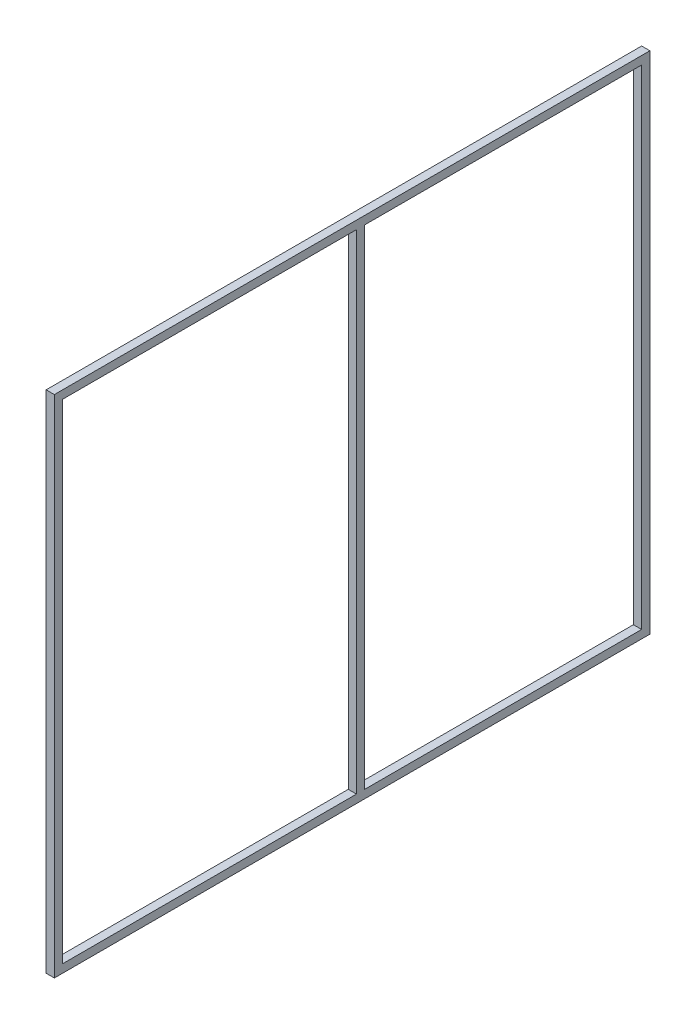
SolidWorks part; units mm, degrees
ref_plane "Front Plane" through (0, 0, 0) normal (0, 0, 1) x (1, 0, 0)
ref_plane "Top Plane" through (0, 0, 0) normal (0, 1, 0) x (1, 0, 0)
ref_plane "Right Plane" through (0, 0, 0) normal (1, 0, 0) x (0, 0, -1)
sketch "Sketch1" plane through (0, 0, 0) normal (1, 0, 0) x (0, 0, -1)
  line L0 (-559.125, -472.0175) -> (-559.125, 472.0175)
  line L2 (-575, -487.8925) -> (-575, 487.8925)
  line L3 (-575, 487.8925) -> (575, 487.8925)
  line L4 (575, -487.8925) -> (575, 487.8925)
  line L5 (-575, -487.8925) -> (575, 487.8925) construction
  line L6 (-575, 487.8925) -> (575, -487.8925) construction
  line L7 (-559.125, 472.0175) -> (559.125, 472.0175)
  line L8 (559.125, -472.0175) -> (559.125, 472.0175)
  line L9 (-575, -487.8925) -> (-559.125, -487.8925)
  line L10 (559.125, -487.8925) -> (575, -487.8925)
  line L11 (-559.125, -487.8925) -> (559.125, -487.8925)
  line L12 (-559.125, -472.0175) -> (559.125, -472.0175)
  line L14 (559.125, -487.8925) -> (559.125, 472.0175) construction
  line L15 (-559.125, -487.8925) -> (-559.125, 472.0175) construction
  point P0 (0, 0)
  point P7 (0, 0)
  dimension "D1" = 1150
  dimension "D2" = 975.785
  dimension "D4" = 15.875
  dimension "D3" = 15.875
extrude "Boss-Extrude1" add sketch "Sketch1" along normal blind 15.875
sketch "Sketch2" [suppressed] plane through (0, -487.8925, 0) normal (0, -1, 0) x (1, 0, 0)
  line L0 (66.5, 469.5) -> (66.5, 555.5) construction
  line L1 (0, 562.5) -> (66.5, 562.5)
  line L2 (0, 562.5) -> (0, 462.5)
  line L3 (0, 462.5) -> (66.5, 462.5)
  line L4 (66.5, 562.5) -> (66.5, 462.5)
  line L5 (89, 512.5) -> (63.5, 512.5) construction
  line L6 (15.875, 546.625) -> (50.625, 546.625)
  line L7 (50.625, 546.625) -> (50.625, 478.375)
  line L8 (15.875, 478.375) -> (50.625, 478.375)
  line L9 (15.875, 546.625) -> (15.875, 478.375)
  line L10 (0, 575) -> (0, -575) construction
  point P7 (66.5, 512.5)
  point P17 (33.25, 462.5)
  dimension "D2" = 100
  dimension "D1" = 15.875
sketch "Sketch3" plane through (0, -472.0175, 0) normal (0, 1, 0) x (1, 0, 0)
  line L0 (15.875, 575) -> (15.875, -575) construction
  line L1 (15.875, 24.3125) -> (0, 24.3125)
  line L2 (15.875, 24.3125) -> (15.875, 8.4375)
  line L3 (15.875, 8.4375) -> (0, 8.4375)
  line L4 (0, 24.3125) -> (0, 8.4375)
  line L5 (0, 575) -> (0, -575) construction
  line L6 (211.75, 24.3125) -> (15.875, 24.3125) construction
  line L7 (211.75, 8.4375) -> (15.875, 8.4375) construction
extrude "Boss-Extrude3" add sketch "Sketch3" along normal up to next
